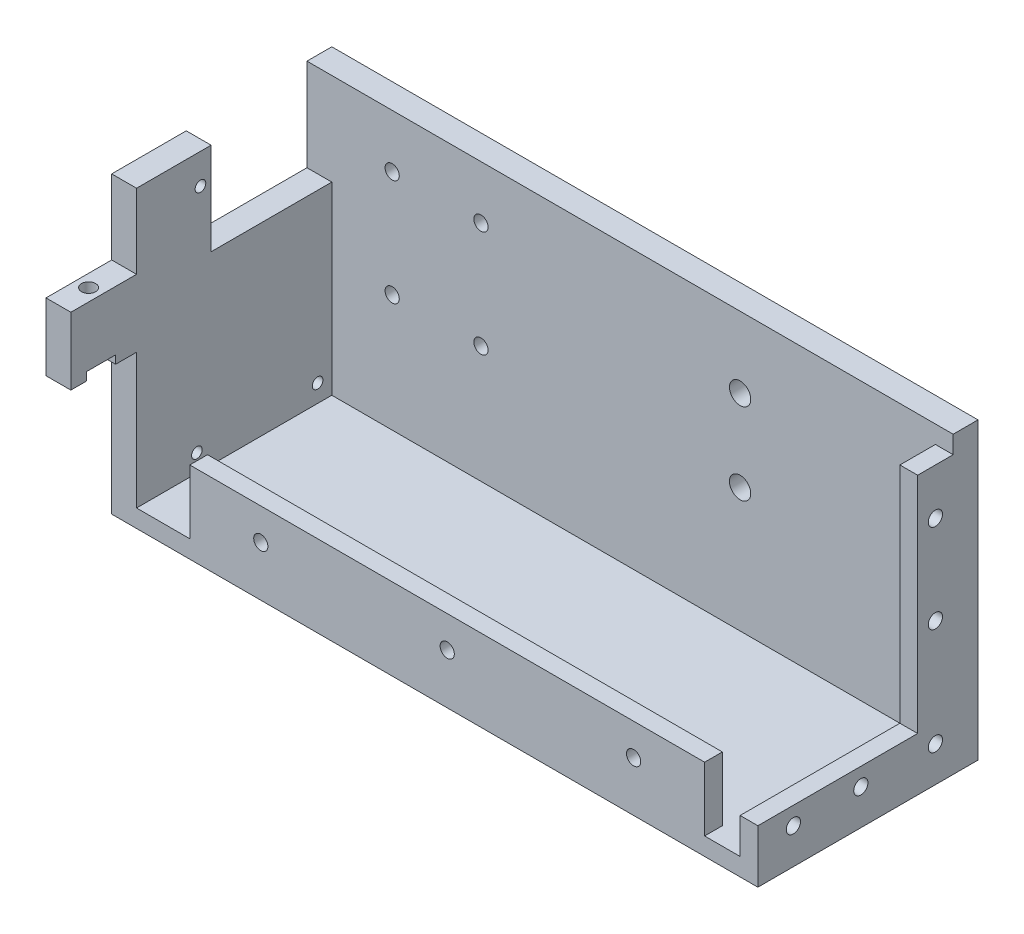
SolidWorks part; units mm, degrees
ref_plane "Front Plane" through (0, 0, 0) normal (0, 0, 1) x (1, 0, 0)
ref_plane "Top Plane" through (0, 0, 0) normal (0, 1, 0) x (1, 0, 0)
ref_plane "Right Plane" through (0, 0, 0) normal (1, 0, 0) x (0, 0, -1)
sketch "Sketch1" plane through (0, 0, 0) normal (0, 1, 0) x (1, 0, 0)
  line L1 (-44.8485, 23.3333) -> (137.1515, 23.3333)
  line L2 (-44.8485, 23.3333) -> (-44.8485, -38.6667)
  line L3 (-44.8485, -38.6667) -> (137.1515, -38.6667)
  line L4 (137.1515, 23.3333) -> (137.1515, -38.6667)
  dimension "D1" = 62
  dimension "D2" = 182
extrude "Boss-Extrude1" add sketch "Sketch1" along normal blind 5
sketch "Sketch2" plane through (0, 5, 0) normal (0, 1, 0) x (1, 0, 0)
  line L0 (-44.8485, -38.6667) -> (137.1515, -38.6667) construction
  line L1 (-22.8485, -38.6667) -> (122.1515, -38.6667)
  line L2 (-22.8485, -38.6667) -> (-22.8485, -33.6667)
  line L3 (-22.8485, -33.6667) -> (122.1515, -33.6667)
  line L4 (122.1515, -38.6667) -> (122.1515, -33.6667)
  line L5 (-44.8485, 23.3333) -> (-44.8485, -38.6667) construction
  line L6 (137.1515, -38.6667) -> (137.1515, 23.3333) construction
  dimension "D1" = 22
  dimension "D2" = 15
  dimension "D3" = 5
extrude "Boss-Extrude2" add sketch "Sketch2" along normal blind 18
sketch "Sketch3" plane through (0, 0, 33.6667) normal (0, 0, -1) x (-1, 0, 0)
  line L0 (-122.1515, 5) -> (22.8485, 5) construction
  line L1 (-122.1515, 23) -> (-122.1515, 5) construction
  line L2 (22.8485, 23) -> (22.8485, 5) construction
  circle A0 centre (-102.1515, 14.1) radius 2
  circle A1 centre (-49.6515, 14.1) radius 2
  circle A2 centre (2.8485, 14.1) radius 2
  dimension "D1" = 9.1
  dimension "D3" = 52.5
  dimension "D5" = 9.1
  dimension "D2" = 20
  dimension "D4" = 20
  dimension "D6" = 52.5
extrude "Cut-Extrude1" cut sketch "Sketch3" against normal blind 18
sketch "Sketch4" plane through (0, 5, 0) normal (0, 1, 0) x (1, 0, 0)
  line L0 (-44.8485, -38.6667) -> (-22.8485, -38.6667) construction
  line L1 (-44.8485, 23.3333) -> (-37.8485, 23.3333)
  line L2 (-44.8485, 23.3333) -> (-44.8485, -38.6667)
  line L3 (-44.8485, -38.6667) -> (-37.8485, -38.6667)
  line L4 (-37.8485, 23.3333) -> (-37.8485, -38.6667)
  dimension "D1" = 7
extrude "Boss-Extrude3" add sketch "Sketch4" along normal blind 78
sketch "Sketch5" plane through (0, 5, 0) normal (0, 1, 0) x (1, 0, 0)
  line L0 (-37.8485, -38.6667) -> (-37.8485, 23.3333) construction
  line L1 (137.1515, 23.3333) -> (-37.8485, 23.3333)
  line L2 (137.1515, 23.3333) -> (137.1515, 16.3333)
  line L3 (137.1515, 16.3333) -> (-37.8485, 16.3333)
  line L4 (-37.8485, 23.3333) -> (-37.8485, 16.3333)
  dimension "D1" = 7
extrude "Boss-Extrude4" add sketch "Sketch5" along normal blind 78
sketch "Sketch6" plane through (0, 0, 38.6667) normal (0, 0, 1) x (1, 0, 0)
  line L0 (-44.8485, 83) -> (-44.8485, 0) construction
  line L1 (-44.8485, 62) -> (-37.8485, 62)
  line L2 (-44.8485, 62) -> (-44.8485, 43)
  line L3 (-44.8485, 43) -> (-37.8485, 43)
  line L4 (-37.8485, 62) -> (-37.8485, 43)
  line L5 (-37.8485, 83) -> (-37.8485, 5) construction
  line L6 (-44.8485, 83) -> (-37.8485, 83) construction
  dimension "D1" = 21
  dimension "D2" = 19
extrude "Boss-Extrude5" add sketch "Sketch6" along normal blind 18.5
sketch "Sketch7" plane through (0, 62, 0) normal (0, 1, 0) x (1, 0, 0)
  line L0 (-44.8485, -38.6667) -> (-37.8485, -38.6667) construction
  line L1 (-44.8485, -57.1667) -> (-44.8485, -38.6667) construction
  circle A0 centre (-41.3485, -48.6667) radius 2
  dimension "D1" = 10
  dimension "D2" = 3.5
extrude "Cut-Extrude2" cut sketch "Sketch7" against normal blind 18 contours A0
sketch "Sketch8" plane through (0, 43, 0) normal (0, -1, 0) x (1, 0, 0)
  line L0 (-44.8485, 57.1667) -> (-44.8485, 38.6667) construction
  line L1 (-44.8485, 52.7667) -> (-37.8485, 52.7667)
  line L2 (-44.8485, 52.7667) -> (-44.8485, 44.5667)
  line L3 (-44.8485, 44.5667) -> (-37.8485, 44.5667)
  line L4 (-37.8485, 52.7667) -> (-37.8485, 44.5667)
  line L5 (-37.8485, 57.1667) -> (-37.8485, 38.6667) construction
  circle A0 centre (-41.3485, 48.6667) radius 2 construction
  dimension "D1" = 8.2
  dimension "D2" = 4.1
extrude "Cut-Extrude3" cut sketch "Sketch8" against normal blind 2.3
sketch "Sketch9" plane through (0, 0, 33.6667) normal (0, 0, -1) x (-1, 0, 0)
  line L0 (-122.1515, 23) -> (-122.1515, 5) construction
  line L1 (-122.1515, 5) -> (22.8485, 5) construction
  circle A0 centre (-102.1515, 14.1) radius 4.4408
  circle A1 centre (-49.6515, 14.1) radius 4.5
  circle A2 centre (2.8485, 14.1) radius 4.5
  dimension "D1" = 52.5
  dimension "D4" = 9.1
  dimension "D5" = 9.1
  dimension "D2" = 20
  dimension "D3" = 9.1
sketch "Sketch11" plane through (-37.8485, 0, 0) normal (1, 0, 0) x (0, 0, -1)
  line L0 (-38.6667, 5) -> (16.3333, 5) construction
  line L1 (16.3333, 83) -> (-17.6667, 83)
  line L2 (16.3333, 83) -> (16.3333, 57)
  line L3 (16.3333, 57) -> (-17.6667, 57)
  line L4 (-17.6667, 83) -> (-17.6667, 57)
  circle A0 centre (-20.6667, 74.5) radius 1.5
  dimension "D3" = 17.5
  dimension "D1" = 52
  dimension "D2" = 34
  dimension "D4" = 3
extrude "Cut-Extrude5" cut sketch "Sketch11" against normal blind 10
sketch "Sketch12" plane through (0, 5, 0) normal (0, 1, 0) x (1, 0, 0)
  line L0 (122.1515, -38.6667) -> (137.1515, -38.6667) construction
  line L1 (137.1515, 16.3333) -> (132.1515, 16.3333)
  line L2 (137.1515, 16.3333) -> (137.1515, -38.6667)
  line L3 (137.1515, -38.6667) -> (132.1515, -38.6667)
  line L4 (132.1515, 16.3333) -> (132.1515, -38.6667)
  dimension "D1" = 5
extrude "Boss-Extrude6" add sketch "Sketch12" along normal blind 10
sketch "Sketch13" plane through (0, 15, 0) normal (0, 1, 0) x (1, 0, 0)
  line L0 (132.1515, 16.3333) -> (132.1515, -38.6667) construction
  line L1 (137.1515, 16.3333) -> (132.1515, 16.3333)
  line L2 (137.1515, 16.3333) -> (137.1515, 6.3333)
  line L3 (137.1515, 6.3333) -> (132.1515, 6.3333)
  line L4 (132.1515, 16.3333) -> (132.1515, 6.3333)
  dimension "D1" = 10
extrude "Boss-Extrude7" add sketch "Sketch13" along normal blind 63
sketch "Sketch15" plane through (137.1515, 0, 0) normal (1, 0, 0) x (0, 0, -1)
  line L0 (-38.6667, 15) -> (-38.6667, 0) construction
  line L1 (-38.6667, 0) -> (23.3333, 0) construction
  line L2 (23.3333, 83) -> (23.3333, 0) construction
  circle A0 centre (11.3333, 65) radius 2
  circle A1 centre (11.3333, 40) radius 2
  circle A2 centre (11.3333, 10) radius 2
  circle A3 centre (-28.6667, 10) radius 2
  circle A4 centre (-9.6667, 10) radius 2
  dimension "D1" = 10
  dimension "D2" = 10
  dimension "D3" = 10
  dimension "D4" = 10
  dimension "D5" = 12
  dimension "D6" = 19
  dimension "D7" = 21
  dimension "D8" = 30
  dimension "D9" = 25
  dimension "D10" = 12
  dimension "D11" = 12
extrude "Cut-Extrude6" cut sketch "Sketch15" against normal blind 63
sketch "Sketch16" plane through (0, 0, -23.3333) normal (0, 0, -1) x (-1, 0, 0)
  line L0 (44.8485, 83) -> (44.8485, 0) construction
  line L1 (-137.1515, 83) -> (44.8485, 83) construction
  circle A0 centre (-77.1515, 40) radius 3
  circle A1 centre (-77.1515, 63) radius 3
  dimension "D1" = 122
  dimension "D2" = 0
  dimension "D3" = 20
  dimension "D4" = 23
extrude "Cut-Extrude7" cut sketch "Sketch16" against normal blind 10
sketch "Sketch17" plane through (0, 0, -23.3333) normal (0, 0, -1) x (-1, 0, 0)
  line L0 (44.8485, 83) -> (44.8485, 0) construction
  line L1 (-137.1515, 83) -> (44.8485, 83) construction
  circle A0 centre (20.8485, 68) radius 2
  circle A1 centre (20.8485, 38) radius 2
  circle A2 centre (-4.1515, 38) radius 2
  circle A3 centre (-4.1515, 68) radius 2
  dimension "D1" = 24
  dimension "D2" = 15
  dimension "D3" = 15
  dimension "D4" = 25
  dimension "D5" = 30
  dimension "D6" = 30
  dimension "D7" = 25
  dimension "D8" = 0
extrude "Cut-Extrude8" cut sketch "Sketch17" against normal blind 10
sketch "Sketch18" plane through (-37.8485, 0, 0) normal (1, 0, 0) x (0, 0, -1)
  line L0 (16.3333, 57) -> (16.3333, 5) construction
  line L1 (-38.6667, 5) -> (16.3333, 5) construction
  circle A0 centre (12.3333, 10) radius 1.5
  circle A1 centre (-21.6667, 10) radius 1.5
  dimension "D1" = 4
  dimension "D3" = 34
  dimension "D2" = 5
extrude "Cut-Extrude9" cut sketch "Sketch18" against normal blind 10
